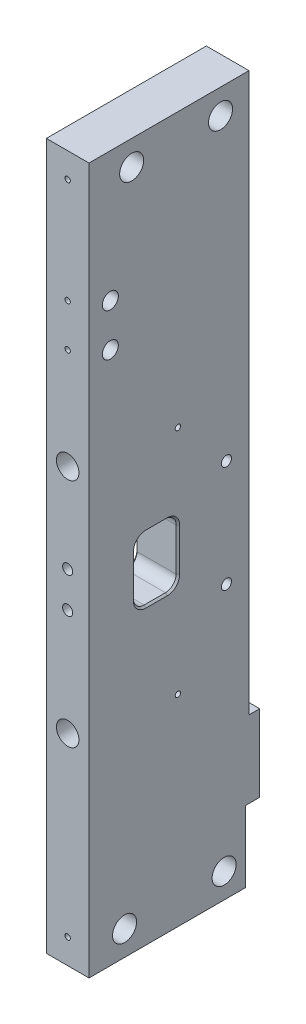
SolidWorks part; units mm, degrees
material "6061-T6 Al"
ref_plane "Front" through (0, 0, 0) normal (0, 0, 1) x (1, 0, 0)
ref_plane "Top" through (0, 0, 0) normal (0, 1, 0) x (1, 0, 0)
ref_plane "Right" through (0, 0, 0) normal (1, 0, 0) x (0, 0, -1)
sketch "Sketch1" plane through (0, 0, 0) normal (1, 0, 0) x (0, 0, -1)
  line L1 (0, 0) -> (-48, 0)
  line L2 (0, 0) -> (0, 198.5)
  line L3 (0, 198.5) -> (-48, 198.5)
  line L4 (-48, 0) -> (-48, 198.5)
  dimension "D1" = 198.5
  dimension "D2" = 48
extrude "Extrude1" add sketch "Sketch1" along normal blind 12
sketch "Sketch2" plane through (12, 0, 0) normal (1, 0, 0) x (0, 0, -1)
  line L0 (-48, 0) -> (0, 0) construction
  line L1 (0, 198.5) -> (-3, 198.5)
  line L2 (0, 198.5) -> (0, 41.6)
  line L3 (0, 41.6) -> (-3, 41.6)
  line L4 (-3, 198.5) -> (-3, 41.6)
  dimension "D1" = 41.6
  dimension "D2" = 3
extrude "Extrude2" cut sketch "Sketch2" against normal through all
sketch "Sketch3" plane through (12, 0, 0) normal (1, 0, 0) x (0, 0, -1)
  line L0 (-48, 198.5) -> (-48, 0) construction
  line L1 (-3, 198.5) -> (-48, 198.5) construction
  line L2 (-48, 0) -> (0, 0) construction
  circle A0 centre (-36, 191.5) radius 3.3782
  circle A1 centre (-11, 191.5) radius 3.3782
  circle A2 centre (-38, 7) radius 3.3782
  circle A3 centre (-10, 7) radius 3.3782
  circle A4 centre (-23, 56.6) radius 0.75
  circle A5 centre (-23, 121.6) radius 0.75
  dimension "D3" = 6.7564
  dimension "D4" = 6.7564
  dimension "D5" = 6.7564
  dimension "D6" = 6.7564
  dimension "D14" = 1.5
  dimension "D15" = 1.5
  dimension "D1" = 12
  dimension "D2" = 25
  dimension "D7" = 7
  dimension "D8" = 7
  dimension "D9" = 28
  dimension "D10" = 10
  dimension "D11" = 25
  dimension "D12" = 56.6
  dimension "D13" = 121.6
extrude "Extrude3" cut sketch "Sketch3" against normal through all
sketch "Sketch4" plane through (12, 0, 0) normal (1, 0, 0) x (0, 0, -1)
  line L0 (-48, 198.5) -> (-48, 0) construction
  line L1 (-35, 100.6) -> (-23, 100.6)
  line L2 (-35, 100.6) -> (-35, 82.6)
  line L3 (-35, 82.6) -> (-23, 82.6)
  line L4 (-23, 100.6) -> (-23, 82.6)
  line L5 (-48, 0) -> (0, 0) construction
  dimension "D1" = 25
  dimension "D2" = 82.6
  dimension "D3" = 18
  dimension "D4" = 12
extrude "Extrude4" cut sketch "Sketch4" against normal through all
fillet "Fillet1" radius 3 4 edges at (6, 100.6, 35) (6, 100.6, 23) (6, 82.6, 23) (6, 82.6, 35)
chamfer "Chamfer1" distance 0.5 angle 45 16 edges at (0, 83.4787, 34.1213) (0, 91.6, 35) (0, 99.7213, 34.1213) (0, 100.6, 29) (0, 99.7213, 23.8787) (0, 82.6, 29) (0, 83.4787, 23.8787) (0, 91.6, 23) (12, 83.4787, 34.1213) (12, 91.6, 35) (12, 99.7213, 34.1213) (12, 100.6, 29) (12, 99.7213, 23.8787) (12, 82.6, 29) (12, 83.4787, 23.8787) (12, 91.6, 23)
sketch "Sketch5" plane through (0, 0, 0) normal (0, -1, 0) x (1, 0, 0)
  line L0 (0, 0) -> (4, 0)
  line L1 (12, 0) -> (0, 0) construction
  line L2 (4, 0) -> (0, 4)
  line L3 (0, 48) -> (0, 0) construction
  line L4 (0, 4) -> (0, 0)
extrude "Extrude5" cut sketch "Sketch5" against normal blind 20
ref_plane "Plane1" through (6, 0, 0) normal (1, 0, 0) x (0, 0, -1)
mirror "Mirror1" about plane through (6, 0, 0) normal (1, 0, 0) of "Extrude5"
hole_wizard "#4-40 Tapped Hole1" positions "3DSketch1" profile "Sketch6" tap size "#4-40" standard "Ansi Inch" end condition through all
sketch3d "3DSketch1"
  line L0 (12, 0, 48) -> (12, 0, 4) construction
  line L1 (12, 198.5, 3) -> (12, 41.6, 3) construction
  point P0 (12, 106.6, 9.35)
  point P2 (12, 76.6, 9.35)
  dimension "D1" = 30
  dimension "D2" = 76.6
  dimension "D3" = 6.35
sketch "Sketch6" plane through (12, 106.6, 9.35) normal (0, 1, 0) x (0, 0, -1)
  line L0 (0, 0) -> (0, 12)
  line L1 (0, 12) -> (1.4224, 12)
  line L2 (1.4224, 12) -> (1.4224, 0)
  line L5 (1.4224, 0) -> (0, 0)
  line L11 (0, -6.35) -> (0, 107.95) construction
  dimension "Thread Major Dia." = 2.8448
  dimension "Thru Tap Drill Depth" = 12
hole_wizard "#4-40 Tapped Hole2" positions "3DSketch2" profile "Sketch7" tap size "#4-40" standard "Ansi Inch"
sketch3d "3DSketch2"
  line L0 (12, 0, 48) -> (0, 0, 48) construction
  line L1 (12, 198.5, 48) -> (12, 0, 48) construction
  point P0 (6, 96.6, 48)
  point P2 (6, 86.6, 48)
  dimension "D1" = 10
  dimension "D2" = 86.6
  dimension "D3" = 6
sketch "Sketch7" plane through (6, 96.6, 48) normal (1, 0, 0) x (0, -1, 0)
  line L0 (0, 0) -> (0, 13.3538)
  line L1 (0, 13.3538) -> (1.1303, 12.6746)
  line L2 (1.1303, 12.6746) -> (1.1303, 5.6896)
  line L3 (1.1303, 5.6896) -> (1.4224, 5.6896)
  line L4 (1.4224, 5.6896) -> (1.4224, 0)
  line L5 (1.4224, 0) -> (0, 0)
  line L10 (0, 13.3538) -> (-1.1303, 12.6746) construction
  line L11 (0, -6.35) -> (0, 107.95) construction
  dimension "Tap Drill Dia." = 2.2606
  dimension "Tap Drill Depth" = 12.6746
  dimension "Thread Major Dia." = 2.8448
  dimension "Thread Depth" = 5.6896
  dimension "Drill Angle" = 118
hole_wizard "1/4-20 Tapped Hole1" positions "3DSketch3" profile "Sketch8" tap size "1/4-20" standard "Ansi Inch" end condition through all
sketch3d "3DSketch3"
  line L0 (12, 0, 48) -> (0, 0, 48) construction
  line L1 (12, 198.5, 48) -> (12, 0, 48) construction
  point P0 (6, 121.6, 48)
  point P2 (6, 56.6, 48)
  dimension "D1" = 56.6
  dimension "D2" = 121.6
  dimension "D3" = 6
sketch "Sketch8" plane through (6, 121.6, 48) normal (1, 0, 0) x (0, -1, 0)
  line L0 (0, 0) -> (0, 48)
  line L1 (0, 48) -> (3.175, 48)
  line L2 (3.175, 48) -> (3.175, 0)
  line L5 (3.175, 0) -> (0, 0)
  line L11 (0, -6.35) -> (0, 107.95) construction
  dimension "Thread Major Dia." = 6.35
  dimension "Thru Tap Drill Depth" = 48
sketch "Sketch9" plane through (0, 0, 48) normal (0, 0, 1) x (1, 0, 0)
  line L0 (12, 198.5) -> (12, 0) construction
  line L1 (12, 0) -> (0, 0) construction
  line L2 (12, 198.5) -> (0, 198.5) construction
  circle A0 centre (6, 7) radius 0.75
  circle A1 centre (6, 191.5) radius 0.75
  dimension "D1" = 1.5
  dimension "D2" = 1.5
  dimension "D3" = 6
  dimension "D4" = 7
  dimension "D5" = 7
extrude "Extrude6" cut sketch "Sketch9" against normal blind 8
sketch "Sketch10" plane through (0, 0, 3) normal (0, 0, -1) x (-1, 0, 0)
  line L0 (0, 198.5) -> (0, 41.6) construction
  line L1 (0, 198.5) -> (-12, 198.5) construction
  circle A0 centre (-6, 191.5) radius 0.75
  dimension "D1" = 1.5
  dimension "D2" = 6
  dimension "D3" = 7
extrude "Extrude7" cut sketch "Sketch10" against normal blind 8
sketch "Sketch12" plane through (0, 0, 0) normal (0, 0, -1) x (-1, 0, 0)
  line L0 (-8, 0) -> (-4, 0) construction
  line L1 (0, 20) -> (0, 41.6) construction
  circle A0 centre (-6, 7) radius 0.75
  dimension "D1" = 1.5
  dimension "D2" = 7
  dimension "D3" = 6
extrude "Extrude8" cut sketch "Sketch12" against normal blind 8
sketch "Sketch13" plane through (12, 0, 0) normal (1, 0, 0) x (0, 0, -1)
  line L0 (-48, 198.5) -> (-48, 0) construction
  line L1 (-48, 0) -> (-4, 0) construction
  circle A0 centre (-42, 162) radius 2.25
  circle A1 centre (-42, 150) radius 2.25
  dimension "D1" = 4.5
  dimension "D2" = 4.5
  dimension "D3" = 6
  dimension "D4" = 150
  dimension "D5" = 12
extrude "Cut-Extrude1" cut sketch "Sketch13" against normal through all
sketch "Sketch14" plane through (0, 0, 48) normal (0, 0, 1) x (1, 0, 0)
  line L0 (6, -24.75) -> (6, 24.75) construction
  line L1 (12, 0) -> (0, 0) construction
  circle A0 centre (6, 162) radius 0.75
  circle A1 centre (6, 150) radius 0.75
  dimension "D1" = 1.5
  dimension "D2" = 1.5
  dimension "D3" = 150
  dimension "D4" = 12
extrude "Cut-Extrude2" cut sketch "Sketch14" against normal blind 6
ref_plane "Plane2" through (0, 0, 29) normal (0, 0, -1) x (-1, 0, 0)
equation "\"D4@Sketch3\" = \"D3@Sketch3\""
equation "\"D5@Sketch3\" = \"D3@Sketch3\""
equation "\"D6@Sketch3\" = \"D3@Sketch3\""
equation "\"D15@Sketch3\" = \"D14@Sketch3\""
equation "\"D2@Sketch9\" = \"D1@Sketch9\""
